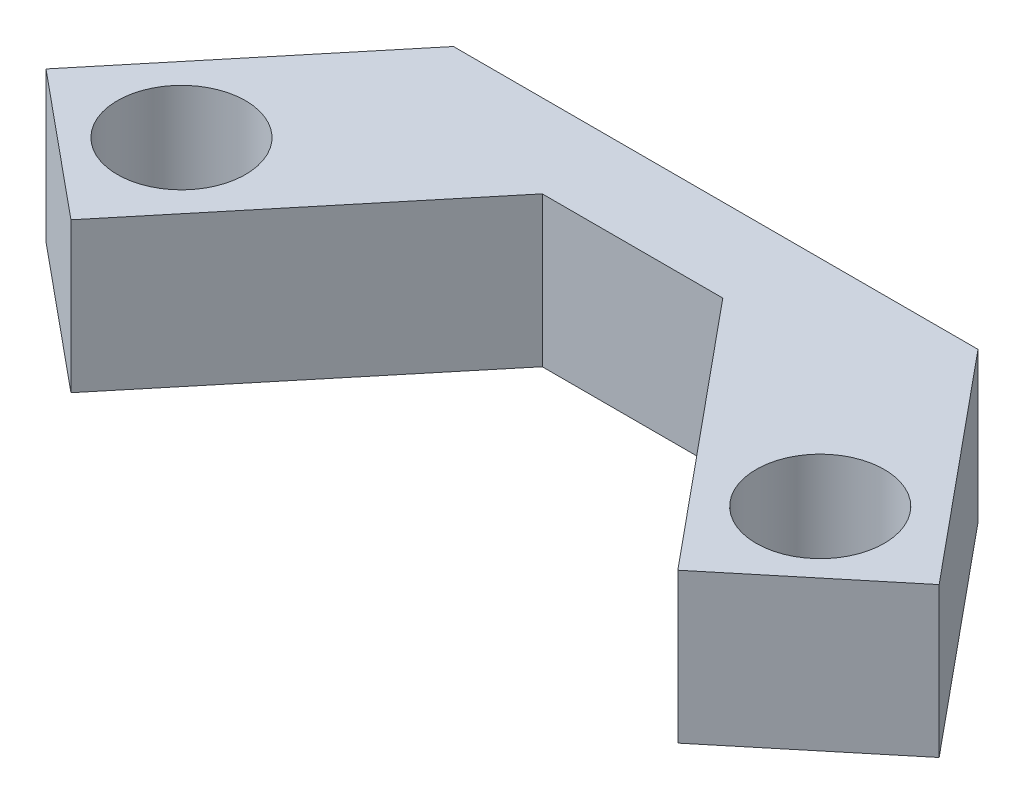
SolidWorks part; units mm, degrees
ref_plane "Front Plane" through (0, 0, 0) normal (0, 0, 1) x (1, 0, 0)
ref_plane "Top Plane" through (0, 0, 0) normal (0, 1, 0) x (1, 0, 0)
ref_plane "Right Plane" through (0, 0, 0) normal (1, 0, 0) x (0, 0, -1)
sketch "Sketch8" plane through (0, 0, 0) normal (0, 1, 0) x (1, 0, 0)
  line L0 (-33.2383, 15.2291) -> (29.8117, 15.2291)
  line L1 (29.8117, 15.2291) -> (51.9637, -11.5943)
  line L2 (51.9637, -11.5943) -> (34.762, -25.8002)
  line L3 (34.762, -25.8002) -> (9.1366, 5.2291)
  line L4 (9.1366, 5.2291) -> (-12.5631, 5.2291)
  line L5 (-1.7133, 15.2291) -> (-1.7133, 5.2291) construction
  line L6 (43.3628, -18.6972) -> (15.3449, 15.2291) construction
  line L7 (-46.7893, -18.6972) -> (-18.7715, 15.2291) construction
  line L8 (-38.1885, -25.8002) -> (-12.5631, 5.2291)
  line L9 (-55.3902, -11.5943) -> (-38.1885, -25.8002)
  line L10 (-33.2383, 15.2291) -> (-55.3902, -11.5943)
  line L11 (-1.7133, 5.2291) -> (-1.7133, -33.9194) construction
  circle A1 centre (36.6767, -10.6012) radius 7.7
  circle A2 centre (-40.1033, -10.6012) radius 7.7
  point P10 (34.3851, -23.8683)
  point P11 (0, 0)
  point P12 (0, 0)
  dimension "D3" = 15.4
  dimension "D5" = 10.5
  dimension "D6" = 33.5
  dimension "D1" = 31.525
  dimension "D2" = 10
  dimension "D4" = 38.39
extrude "Boss-Extrude4" add sketch "Sketch8" along normal blind 18
